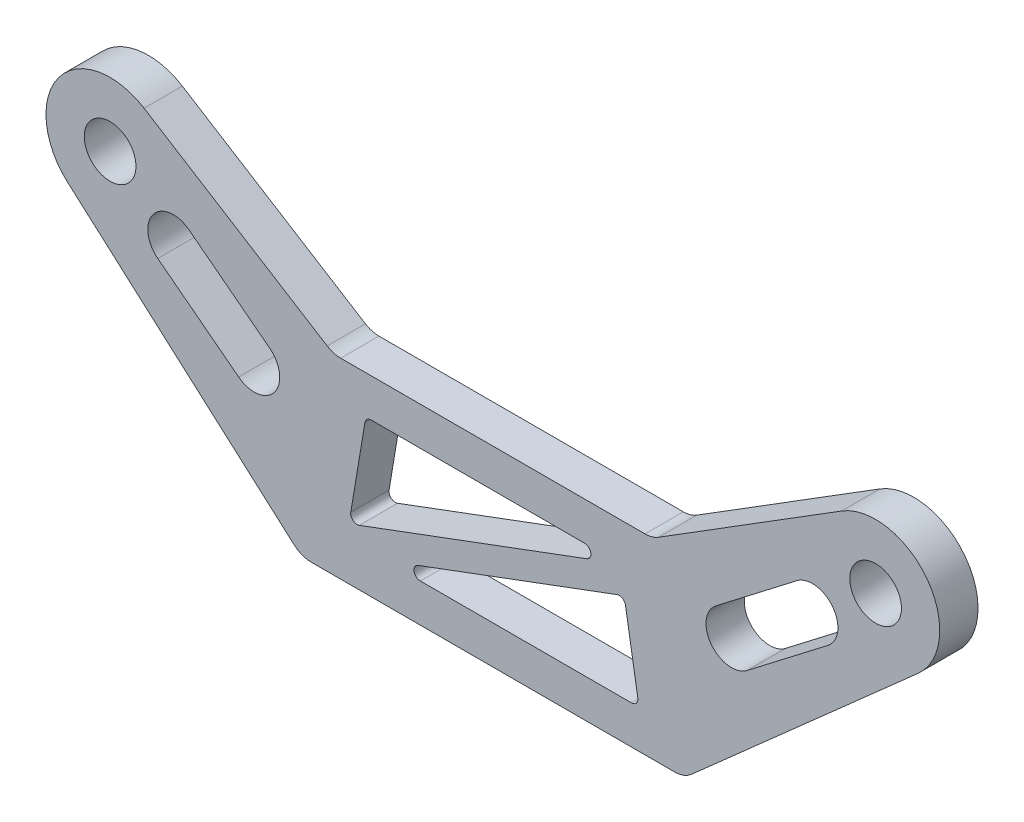
SolidWorks part; units mm, degrees
material "A-玻璃纤维"
ref_plane "前视基准面" through (0, 0, 0) normal (0, 0, 1) x (1, 0, 0)
ref_plane "上视基准面" through (0, 0, 0) normal (0, 1, 0) x (1, 0, 0)
ref_plane "右视基准面" through (0, 0, 0) normal (1, 0, 0) x (0, 0, -1)
other "Configuration Table"
sketch "草图1" plane through (0, 0, 0) normal (0, 0, 1) x (1, 0, 0)
  line L0 (-30, 0) -> (30, 0) construction
  line L1 (-33.3319, -3.7615) -> (-15, -20)
  line L2 (-15, -20) -> (15, -20)
  line L3 (15, -20) -> (33.3319, -3.7615)
  line L4 (0, 0) -> (0, 30.5) construction
  line L5 (-27.3392, 4.2627) -> (-12.5, -5)
  line L6 (-12.5, -5) -> (12.5, -5)
  line L7 (12.5, -5) -> (27.3392, 4.2627)
  circle A0 centre (-30, 0) radius 2.025
  circle A1 centre (30, 0) radius 2.025
  circle A2 centre (-30, 0) radius 5.025
  circle A3 centre (30, 0) radius 5.025
  circle A4 centre (0, 30.5) radius 33.35 construction
  point P4 (0, 0)
  point P20 (-10.6271, -4.2193)
  point P21 (-11.7049, -5)
  dimension "D1" = 4.05
  dimension "D3" = 3
  dimension "D5" = 66.7
  dimension "D2" = 60
  dimension "D4" = 30.5
  dimension "D6" = 5
  dimension "D7" = 25
  dimension "D8" = 15
  dimension "D9" = 30
extrude "凸台-拉伸1" add sketch "草图1" along normal blind 3 contours A2 A0 | A3 L7 L6 L5 A2 L1 L2 L3 | A3 A1
sketch "草图2" plane through (0, 0, 3) normal (0, 0, 1) x (1, 0, 0)
  line L0 (-12.5, -5) -> (-15, -20) construction
  line L1 (12.5, -5) -> (15, -20) construction
  line L2 (9.9586, -8) -> (-9.9586, -8)
  line L3 (-9.9586, -8) -> (-11.278, -15.9166)
  line L4 (-11.278, -15.9166) -> (9.9586, -8)
  line L5 (10.2936, -10.0096) -> (-8.4586, -17)
  line L6 (-8.4586, -17) -> (11.4586, -17)
  line L7 (11.4586, -17) -> (10.2936, -10.0096)
  line L8 (-12.5, -5) -> (12.5, -5) construction
  line L9 (-15, -20) -> (15, -20) construction
  line L10 (9.9586, -8) -> (10.2936, -10.0096) construction
  line L11 (-30, 0) -> (-13.75, -12.5) construction
  line L12 (30, 0) -> (13.75, -12.5)
  line L13 (-25.0455, -3.8112) -> (-18.7045, -8.6888) construction
  line L16 (18.7045, -8.6888) -> (25.0455, -3.8112) construction
  line L17 (17.4851, -7.1036) -> (23.8261, -2.2259)
  line L18 (19.9239, -10.2741) -> (26.2649, -5.3964)
  line L19 (-23.8261, -2.2259) -> (-17.4851, -7.1036)
  line L20 (-26.2649, -5.3964) -> (-19.9239, -10.2741)
  arc A2 (17.4851, -7.1036) -> (19.9239, -10.2741) centre (18.7045, -8.6888) ccw
  arc A3 (26.2649, -5.3964) -> (23.8261, -2.2259) centre (25.0455, -3.8112) ccw
  arc A4 (-23.8261, -2.2259) -> (-26.2649, -5.3964) centre (-25.0455, -3.8112) ccw
  arc A5 (-19.9239, -10.2741) -> (-17.4851, -7.1036) centre (-18.7045, -8.6888) ccw
  point P26 (-21.875, -6.25)
  point P32 (21.875, -6.25)
  dimension "D7" = 2
  dimension "D1" = 3
  dimension "D2" = 3
  dimension "D3" = 2
  dimension "D4" = 3
  dimension "D5" = 3
  dimension "D6" = 8
extrude "切除-拉伸1" cut sketch "草图2" against normal blind 13 contours L20 A5 L19 A4 | L3 L4 L2 | L6 L7 L5 | L18 A3 L12 A2
fillet "圆角1" radius 0.5 6 edges at (9.9586, -8, 1.5) (-11.278, -15.9166, 1.5) (-9.9586, -8, 1.5) (10.2936, -10.0096, 1.5) (-8.4586, -17, 1.5) (11.4586, -17, 1.5)
fillet "圆角2" radius 2 4 edges at (-12.5, -5, 1.5) (15, -20, 1.5) (-15, -20, 1.5) (12.5, -5, 1.5)
